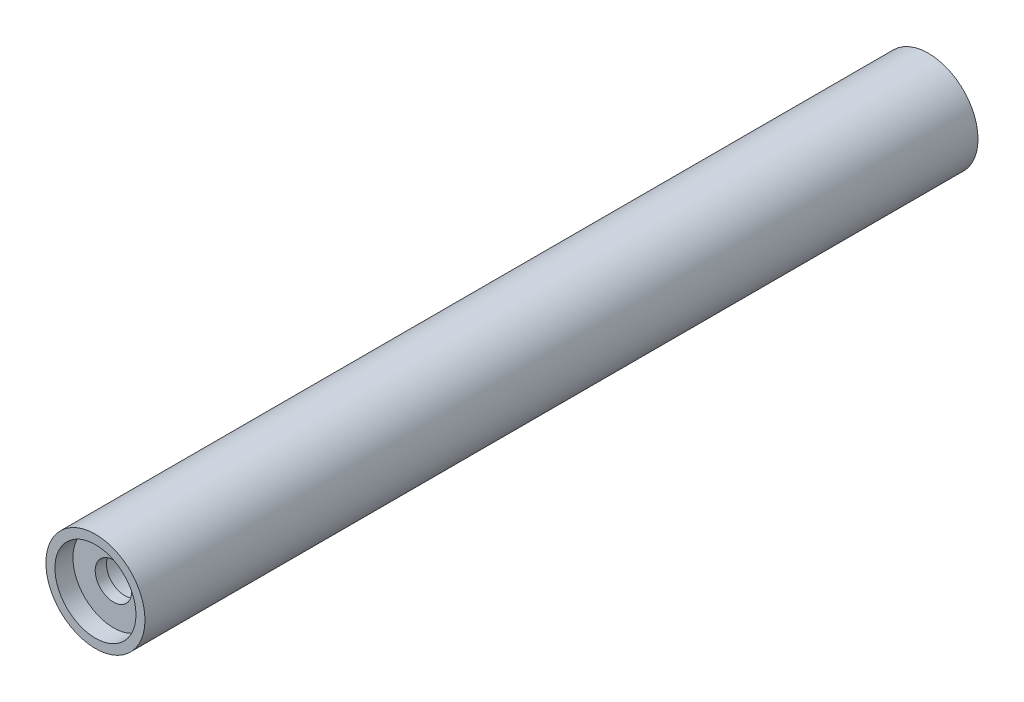
SolidWorks part; units mm, degrees
ref_plane "Front Plane" through (0, 0, 0) normal (0, 0, 1) x (1, 0, 0)
ref_plane "Top Plane" through (0, 0, 0) normal (0, 1, 0) x (1, 0, 0)
ref_plane "Right Plane" through (0, 0, 0) normal (1, 0, 0) x (0, 0, -1)
sketch "Sketch1" plane through (0, 0, 0) normal (0, 0, 1) x (1, 0, 0)
  circle A0 centre (0, 0) radius 5.5
  circle A1 centre (0, 0) radius 2.025
  dimension "D1" = 11
  dimension "D2" = 4.05
extrude "Boss-Extrude1" add sketch "Sketch1" along normal blind 92.5
sketch "Sketch2" plane through (0, 0, 92.5) normal (0, 0, 1) x (1, 0, 0)
  circle A0 centre (0, 0) radius 4.5
  dimension "D1" = 9
extrude "Cut-Extrude1" cut sketch "Sketch2" against normal blind 2
sketch "Sketch3" plane through (0, 0, 0) normal (0, 0, -1) x (-1, 0, 0)
  circle A0 centre (0, 0) radius 4.5
  dimension "D1" = 9
extrude "Cut-Extrude2" cut sketch "Sketch3" against normal blind 2
ref_plane "Plane1" through (0, 0, 46.25) normal (0, 0, 1) x (1, 0, 0)
sketch "Sketch4" plane through (0, 0, 46.25) normal (0, 0, 1) x (1, 0, 0)
  circle A0 centre (0, 0) radius 3
  dimension "D1" = 6
extrude "Cut-Extrude3" cut sketch "Sketch4" against normal mid plane 86 contours A0
